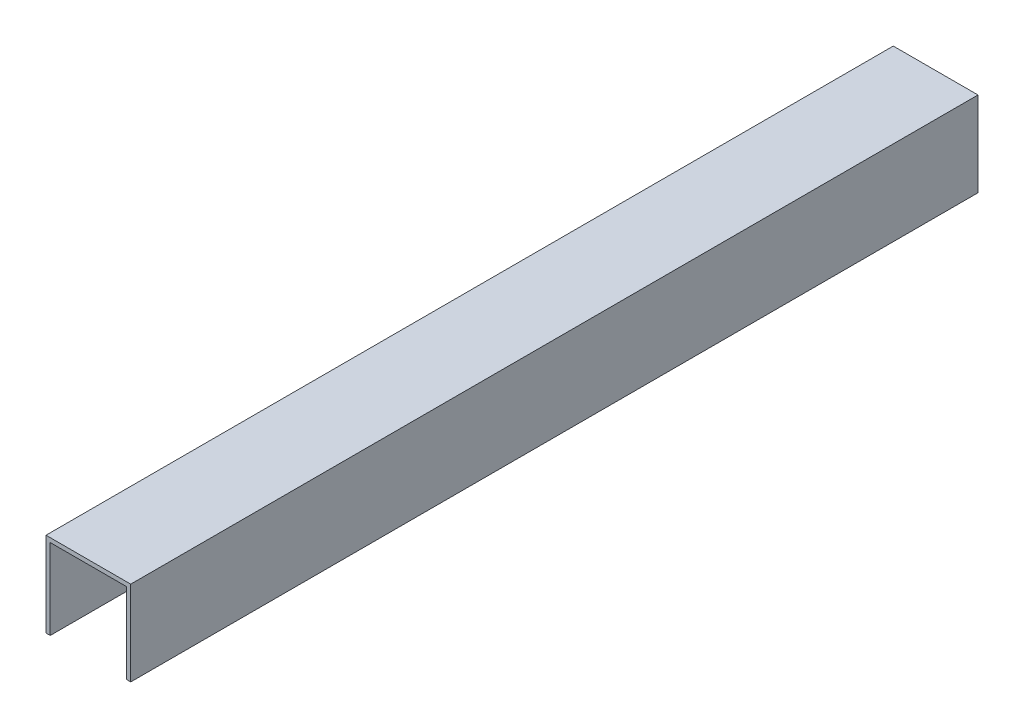
SolidWorks part; units mm, degrees
ref_plane "Plan de face" through (0, 0, 0) normal (0, 0, 1) x (1, 0, 0)
ref_plane "Plan de dessus" through (0, 0, 0) normal (0, 1, 0) x (1, 0, 0)
ref_plane "Plan de droite" through (0, 0, 0) normal (1, 0, 0) x (0, 0, -1)
sketch "Esquisse2" plane through (0, 0, 0) normal (0, 0, 1) x (1, 0, 0)
  line L0 (-107.4415, -9.2332) -> (-107.4415, 0.7668)
  line L1 (-107.4415, 0.7668) -> (-97.4415, 0.7668)
  line L2 (-97.4415, 0.7668) -> (-97.4415, -9.2332)
  line L3 (-97.4415, -9.2332) -> (-97.9415, -9.2332)
  line L4 (-97.9415, -9.2332) -> (-97.9415, 0.2668)
  line L5 (-97.9415, 0.2668) -> (-106.9415, 0.2668)
  line L6 (-106.9415, 0.2668) -> (-106.9415, -9.2332)
  line L7 (-106.9415, -9.2332) -> (-107.4415, -9.2332)
  dimension "D1" = 0.5
  dimension "D2" = 0.5
  dimension "D3" = 0.5
  dimension "D4" = 10
  dimension "D5" = 10
  dimension "D6" = 9
extrude "Boss.-Extru.1" add sketch "Esquisse2" along normal blind 100
